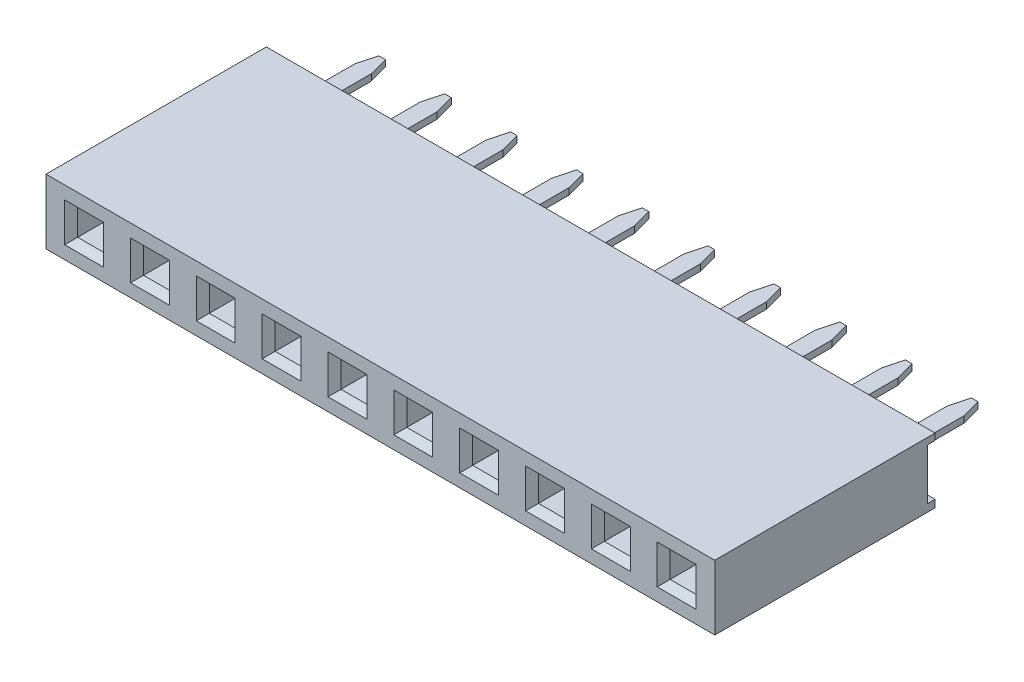
SolidWorks part; units mm, degrees
ref_plane "Front Plane" through (0, 0, 0) normal (0, 0, 1) x (1, 0, 0)
ref_plane "Top Plane" through (0, 0, 0) normal (0, 1, 0) x (1, 0, 0)
ref_plane "Right Plane" through (0, 0, 0) normal (1, 0, 0) x (0, 0, -1)
sketch "Sketch1" plane through (0, 0, 0) normal (0, 0, 1) x (1, 0, 0)
  line L1 (0, 0) -> (25.8, 0)
  line L2 (0, 0) -> (0, 2.5)
  line L3 (0, 2.5) -> (25.8, 2.5)
  line L4 (25.8, 0) -> (25.8, 2.5)
  dimension "width" = 2.5
  dimension "length" = 25.8
extrude "Boss-Extrude1" add sketch "Sketch1" along normal blind 8.5
sketch "Sketch2" plane through (0, 0, 8.5) normal (0, 0, 1) x (1, 0, 0)
  line L0 (0, 1.25) -> (25.8, 1.25) construction
  line L1 (0, 2.5) -> (0, 0) construction
  line L2 (25.8, 0) -> (25.8, 2.5) construction
  line L3 (0, 0) -> (25.8, 0) construction
  line L5 (25.8, 2.5) -> (0, 2.5) construction
  line L6 (1.47, 2.5) -> (1.47, 0) construction
  line L7 (0.97, 1.75) -> (1.97, 1.75)
  line L8 (0.97, 1.75) -> (0.97, 0.75)
  line L9 (0.97, 0.75) -> (1.97, 0.75)
  line L10 (1.97, 1.75) -> (1.97, 0.75)
  point P16 (1.47, 1.75)
  point P17 (1.97, 1.25)
  dimension "D1" = 1.25
  dimension "D2" = 1.47
  dimension "D3" = 1
  dimension "D4" = 1
extrude "Cut-Extrude1" cut sketch "Sketch2" against normal blind 2.25
chamfer "Chamfer1" distance 0.25 angle 45 4 edges at (0.97, 1.25, 8.5) (1.47, 0.75, 8.5) (1.97, 1.25, 8.5) (1.47, 1.75, 8.5)
sketch "Sketch3" plane through (0, 0, 0) normal (-1, 0, 0) x (0, 0, 1)
  line L0 (0, 2.5) -> (0, 0) construction
  line L1 (0, 2.25) -> (0.3, 2.25)
  line L2 (0, 2.25) -> (0, 0.2861)
  line L3 (0, 0.2861) -> (0.3, 0.2861)
  line L4 (0.3, 2.25) -> (0.3, 0.2861)
  line L5 (8.5, 1.25) -> (0, 1.2681) construction
  line L6 (8.5, 2.5) -> (0, 2.5) construction
  line L7 (8.5, 2.5) -> (8.5, 0) construction
  dimension "D1" = 0.25
  dimension "D2" = 0.3
extrude "Cut-Extrude2" cut sketch "Sketch3" against normal through all
ref_plane "Plane1" through (0, 1.25, 0) normal (0, -1, 0) x (-1, 0, 0)
sketch "Sketch4" plane through (0, 1.25, 0) normal (0, -1, 0) x (-1, 0, 0)
  line L0 (-1.47, -8.25) -> (-1.47, -0.3) construction
  line L1 (-0.97, -8.25) -> (-1.97, -8.25) construction
  line L2 (-25.8, -0.3) -> (0, -0.3) construction
  line L3 (0, 0) -> (-25.8, 0) construction
  line L4 (-1.795, -0.3) -> (-1.145, -0.3)
  line L5 (-1.795, -0.3) -> (-1.795, 3)
  line L6 (-1.795, 3) -> (-1.145, 3)
  line L7 (-1.145, -0.3) -> (-1.145, 3)
  point P10 (-1.47, -0.3)
  dimension "D1" = 0.65
  dimension "D2" = 3
extrude "Boss-Extrude2" add sketch "Sketch4" along normal mid plane 0.25 separate body
chamfer "Chamfer2" distance 0.2 angle 75 2 edges at (1.145, 1.25, -3) (1.795, 1.25, -3)
pattern_linear "LPattern4" count 10 spacing 2.54 along (1, 0, 0) of bodies 104
pattern_linear "LPattern5" count 10 spacing 2.54 along (1, 0, 0) of "Cut-Extrude1", "Chamfer1"
equation "\"pins\" = 10"
equation "\"rows\"= 1"
equation "\"length\"= 2.54 * \"pins\" + .4"
equation "\"width\"= 2.5 * \"rows\""
equation "\"width@Sketch1\"= 2.5 * \"rows\""
equation "\"length@Sketch1\"= 2.54 * \"pins\" + .4"
equation "\"D2@LPattern5\"= \"rows\""
equation "\"D2@LPattern4\"= \"rows\""
equation "\"D1@LPattern4\"= \"pins\""
equation "\"D1@LPattern5\"= \"pins\""
